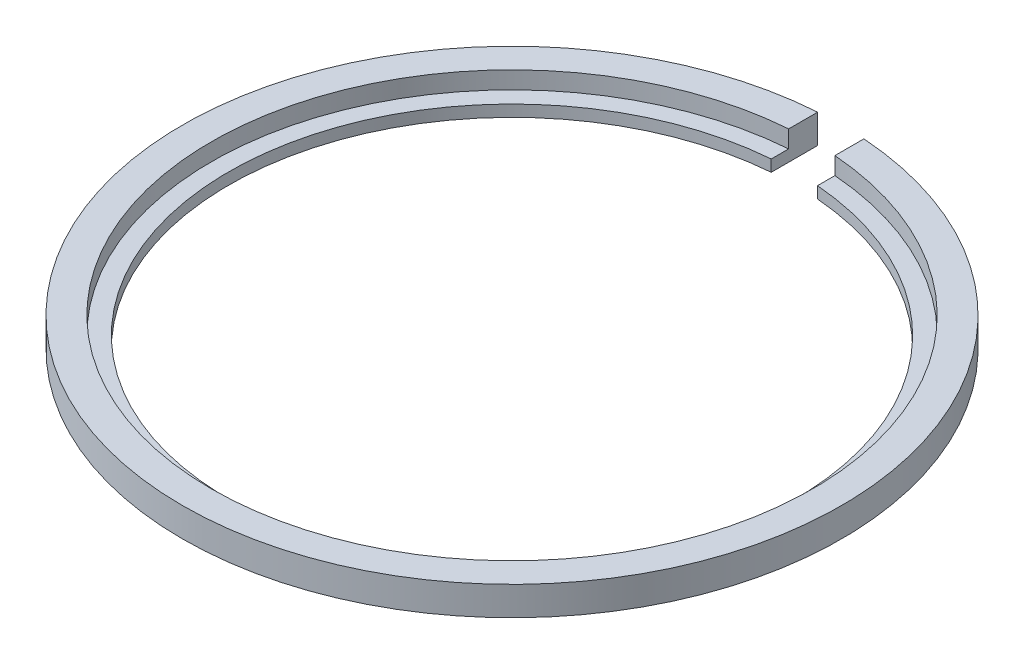
SolidWorks part; units mm, degrees
material "Сталь"
ref_plane "Спереди" through (0, 0, 0) normal (0, 0, 1) x (1, 0, 0)
ref_plane "Сверху" through (0, 0, 0) normal (0, 1, 0) x (1, 0, 0)
ref_plane "Справа" through (0, 0, 0) normal (1, 0, 0) x (0, 0, -1)
sketch "Эскиз1" plane through (0, 0, 0) normal (0, 0, 1) x (1, 0, 0)
  line L0 (0, 27.2585) -> (0, 0) construction
  line L1 (24.5, 0) -> (28.5, 0)
  line L2 (28.5, 0) -> (28.5, 2.5)
  line L3 (28.5, 2.5) -> (26, 2.5)
  line L4 (26, 2.5) -> (26, 1)
  line L5 (26, 1) -> (24.5, 1)
  line L6 (24.5, 1) -> (24.5, 0)
  dimension "D1" = 49
  dimension "D2" = 57
  dimension "D3" = 1
  dimension "D4" = 2.5
  dimension "D5" = 2.5
revolve "Повернуть1" add sketch "Эскиз1" angle 360 about L0
sketch "Эскиз2" plane through (0, 0, 0) normal (0, 1, 0) x (1, 0, 0)
  line L1 (2, 0) -> (-2, 0)
  line L2 (2, 0) -> (2, 52)
  line L3 (2, 52) -> (-2, 52)
  line L4 (-2, 0) -> (-2, 52)
  line L5 (2, 0) -> (-2, 52) construction
  line L6 (2, 52) -> (-2, 0) construction
  circle A0 centre (0, 0) radius 26 construction
  circle A1 centre (0, 0) radius 26 construction
  point P0 (0, 26)
  point P9 (0, 0)
  dimension "D1" = 4
extrude "Вырез-Вытянуть5" cut sketch "Эскиз2" along normal through all contours L4 L1 L2 L3
